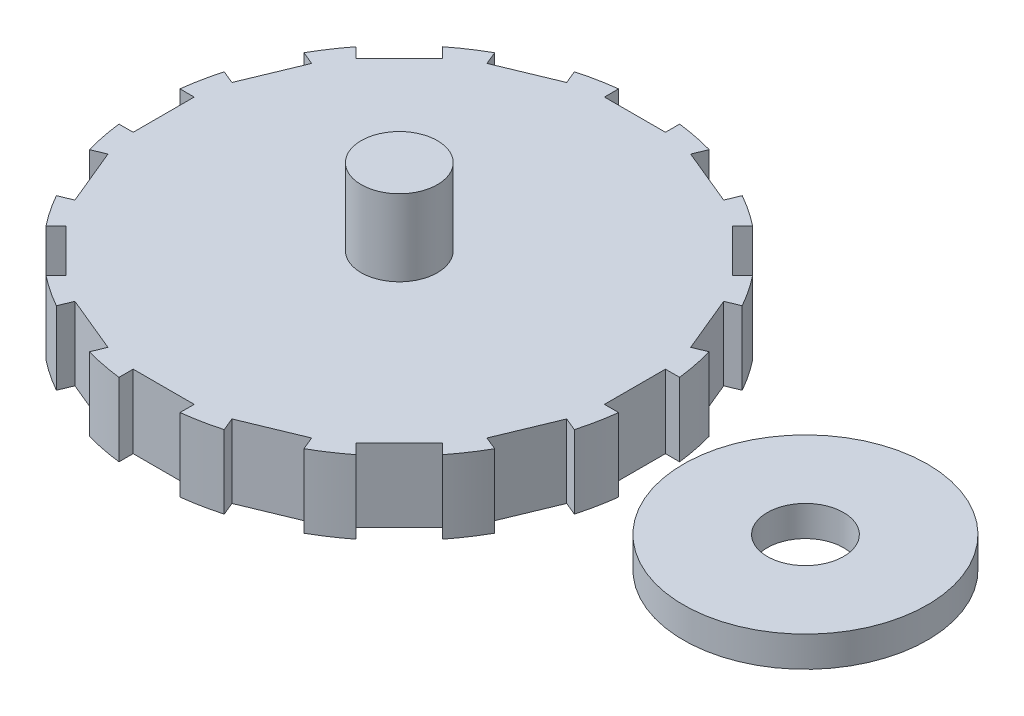
SolidWorks part; units mm, degrees
ref_plane "Front Plane" through (0, 0, 0) normal (0, 0, 1) x (1, 0, 0)
ref_plane "Top Plane" through (0, 0, 0) normal (0, 1, 0) x (1, 0, 0)
ref_plane "Right Plane" through (0, 0, 0) normal (1, 0, 0) x (0, 0, -1)
sketch "Sketch1" plane through (0, 0, 0) normal (0, 1, 0) x (1, 0, 0)
  circle A0 centre (0, 0) radius 8.25
  dimension "D1" = 16.5
extrude "Boss-Extrude1" add sketch "Sketch1" along normal blind 2.4
sketch "Sketch2" plane through (0, 2.4, 0) normal (0, 1, 0) x (1, 0, 0)
  circle A0 centre (0, 0) radius 1.25
  dimension "D1" = 2.5
extrude "Boss-Extrude2" add sketch "Sketch2" along normal blind 2.5
sketch "Sketch3" plane through (0, 0, 0) normal (0, -1, 0) x (1, 0, 0)
  line L1 (-2.5228, 0.1897) -> (2.4772, 0.1897)
  line L2 (-2.5228, 0.1897) -> (-2.5228, -0.2103)
  line L3 (-2.5228, -0.2103) -> (2.4772, -0.2103)
  line L4 (2.4772, 0.1897) -> (2.4772, -0.2103)
  point P4 (2.4772, -0.0103)
  dimension "D1" = 0.4
  dimension "D2" = 5
sketch "Sketch4" plane through (0, 0, 0) normal (0, -1, 0) x (1, 0, 0)
  line L0 (2.626, 8.9528) -> (2.032, 7.5189)
  line L1 (-1, 9.2762) -> (1, 9.2762)
  line L2 (-1, 9.2762) -> (-1, 7.7242)
  line L3 (-1, 7.7242) -> (1, 7.7242)
  line L4 (1, 9.2762) -> (1, 7.7242)
  line L5 (2.626, 8.9528) -> (4.4737, 8.1874)
  line L6 (4.4737, 8.1874) -> (3.8798, 6.7535)
  line L7 (2.032, 7.5189) -> (3.8798, 6.7535)
  line L8 (5.8521, 7.2664) -> (4.7547, 6.1689)
  line L9 (5.8521, 7.2664) -> (7.2664, 5.8521)
  line L10 (7.2664, 5.8521) -> (6.1689, 4.7547)
  line L11 (4.7547, 6.1689) -> (6.1689, 4.7547)
  line L12 (8.1874, 4.4737) -> (6.7535, 3.8798)
  line L13 (8.1874, 4.4737) -> (8.9528, 2.626)
  line L14 (8.9528, 2.626) -> (7.5189, 2.032)
  line L15 (6.7535, 3.8798) -> (7.5189, 2.032)
  line L16 (9.2762, 1) -> (7.7242, 1)
  line L17 (9.2762, 1) -> (9.2762, -1)
  line L18 (9.2762, -1) -> (7.7242, -1)
  line L19 (7.7242, 1) -> (7.7242, -1)
  line L20 (8.9528, -2.626) -> (7.5189, -2.032)
  line L21 (8.9528, -2.626) -> (8.1874, -4.4737)
  line L22 (8.1874, -4.4737) -> (6.7535, -3.8798)
  line L23 (7.5189, -2.032) -> (6.7535, -3.8798)
  line L24 (7.2664, -5.8521) -> (6.1689, -4.7547)
  line L25 (7.2664, -5.8521) -> (5.8521, -7.2664)
  line L26 (5.8521, -7.2664) -> (4.7547, -6.1689)
  line L27 (6.1689, -4.7547) -> (4.7547, -6.1689)
  line L28 (4.4737, -8.1874) -> (3.8798, -6.7535)
  line L29 (4.4737, -8.1874) -> (2.626, -8.9528)
  line L30 (2.626, -8.9528) -> (2.032, -7.5189)
  line L31 (3.8798, -6.7535) -> (2.032, -7.5189)
  line L32 (1, -9.2762) -> (1, -7.7242)
  line L33 (1, -9.2762) -> (-1, -9.2762)
  line L34 (-1, -9.2762) -> (-1, -7.7242)
  line L35 (1, -7.7242) -> (-1, -7.7242)
  line L36 (-2.626, -8.9528) -> (-2.032, -7.5189)
  line L37 (-2.626, -8.9528) -> (-4.4737, -8.1874)
  line L38 (-4.4737, -8.1874) -> (-3.8798, -6.7535)
  line L39 (-2.032, -7.5189) -> (-3.8798, -6.7535)
  line L40 (-5.8521, -7.2664) -> (-4.7547, -6.1689)
  line L41 (-5.8521, -7.2664) -> (-7.2664, -5.8521)
  line L42 (-7.2664, -5.8521) -> (-6.1689, -4.7547)
  line L43 (-4.7547, -6.1689) -> (-6.1689, -4.7547)
  line L44 (-8.1874, -4.4737) -> (-6.7535, -3.8798)
  line L45 (-8.1874, -4.4737) -> (-8.9528, -2.626)
  line L46 (-8.9528, -2.626) -> (-7.5189, -2.032)
  line L47 (-6.7535, -3.8798) -> (-7.5189, -2.032)
  line L48 (-9.2762, -1) -> (-7.7242, -1)
  line L49 (-9.2762, -1) -> (-9.2762, 1)
  line L50 (-9.2762, 1) -> (-7.7242, 1)
  line L51 (-7.7242, -1) -> (-7.7242, 1)
  line L52 (-8.9528, 2.626) -> (-7.5189, 2.032)
  line L53 (-8.9528, 2.626) -> (-8.1874, 4.4737)
  line L54 (-8.1874, 4.4737) -> (-6.7535, 3.8798)
  line L55 (-7.5189, 2.032) -> (-6.7535, 3.8798)
  line L56 (-7.2664, 5.8521) -> (-6.1689, 4.7547)
  line L57 (-7.2664, 5.8521) -> (-5.8521, 7.2664)
  line L58 (-5.8521, 7.2664) -> (-4.7547, 6.1689)
  line L59 (-6.1689, 4.7547) -> (-4.7547, 6.1689)
  line L60 (-4.4737, 8.1874) -> (-3.8798, 6.7535)
  line L61 (-4.4737, 8.1874) -> (-2.626, 8.9528)
  line L62 (-2.626, 8.9528) -> (-2.032, 7.5189)
  line L63 (-3.8798, 6.7535) -> (-2.032, 7.5189)
  point P67 (0, 0)
  dimension "D1" = 1
  dimension "D2" = 1
  dimension "D3" = 16
extrude "Cut-Extrude2" cut sketch "Sketch4" against normal blind 4
sketch "Sketch5" plane through (0, 0, 0) normal (0, -1, 0) x (1, 0, 0)
  circle A0 centre (13.3133, 0) radius 4
  circle A1 centre (13.3133, 0) radius 1.25
  dimension "D1" = 8
  dimension "D2" = 2.5
extrude "Boss-Extrude3" add sketch "Sketch5" against normal blind 1 separate body
